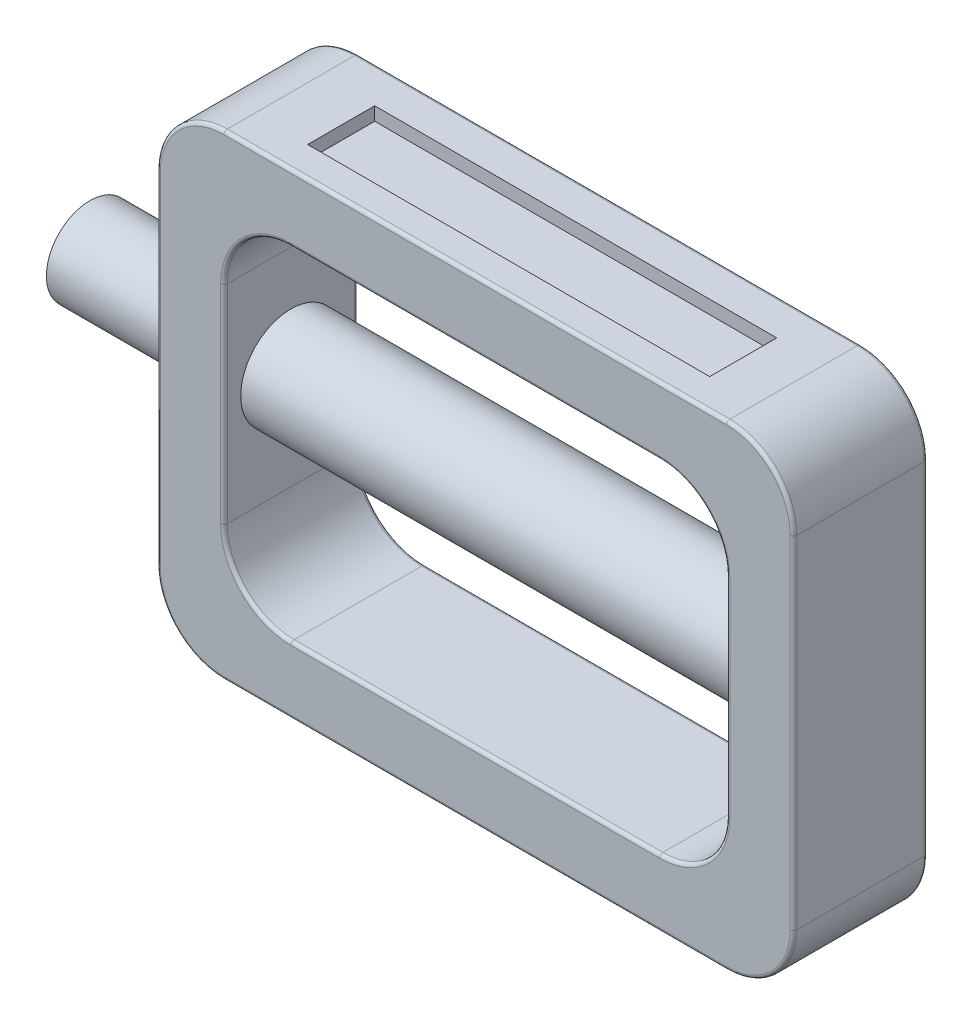
SolidWorks part; units mm, degrees
material "AISI 316 Stainless Steel Sheet (SS)"
ref_plane "Front Plane" through (0, 0, 0) normal (0, 0, 1) x (1, 0, 0)
ref_plane "Top Plane" through (0, 0, 0) normal (0, 1, 0) x (1, 0, 0)
ref_plane "Right Plane" through (0, 0, 0) normal (1, 0, 0) x (0, 0, -1)
sketch "Sketch1" plane through (0, 0, 0) normal (0, 0, 1) x (1, 0, 0)
  line L0 (0, 0) -> (0, 25.5)
  line L1 (10, 35.5) -> (85, 35.5)
  line L2 (95, 25.5) -> (95, -25.5)
  line L3 (85, -35.5) -> (10, -35.5)
  line L4 (0, -25.5) -> (0, 0)
  line L5 (0, 0) -> (95, 0) construction
  line L6 (10, 0) -> (10, 15.5)
  line L7 (20, 25.5) -> (75, 25.5)
  line L8 (85, 15.5) -> (85, 0)
  line L9 (85, 0) -> (85, -15.5)
  line L10 (75, -25.5) -> (20, -25.5)
  line L11 (10, -15.5) -> (10, 0)
  arc A0 (20, -25.5) -> (10, -15.5) centre (20, -15.5) cw
  arc A1 (85, -15.5) -> (75, -25.5) centre (75, -15.5) cw
  arc A2 (75, 25.5) -> (85, 15.5) centre (75, 15.5) cw
  arc A3 (10, 15.5) -> (20, 25.5) centre (20, 15.5) cw
  arc A4 (10, -35.5) -> (0, -25.5) centre (10, -25.5) cw
  arc A5 (95, -25.5) -> (85, -35.5) centre (85, -25.5) cw
  arc A6 (85, 35.5) -> (95, 25.5) centre (85, 25.5) cw
  arc A7 (0, 25.5) -> (10, 35.5) centre (10, 25.5) cw
  point P19 (85, 25.5)
  point P22 (10, 25.5)
  point P25 (0, -35.5)
  point P28 (95, -35.5)
  point P33 (0, 35.5)
  dimension "D6" = 10
  dimension "D1" = 95
  dimension "D2" = 35.5
  dimension "D3" = 25.5
  dimension "D4" = 75
  dimension "D5" = 10
extrude "Boss-Extrude1" add sketch "Sketch1" along normal blind 20
sketch "Sketch2" plane through (0, 0, 0) normal (1, 0, 0) x (0, 0, -1)
  line L0 (-20, 0) -> (0, 0) construction
  line L1 (-10, 25.5) -> (-10, -25.5) construction
  line L2 (-20, 25.5) -> (0, 25.5) construction
  line L3 (-20, -25.5) -> (0, -25.5) construction
  circle A0 centre (-10, 0) radius 7.5
  dimension "D1" = 15
  dimension "D2" = 10
extrude "Boss-Extrude2" add sketch "Sketch2" along normal up to surface (85 mm away) up to face at (85, 0, 10)
sketch "Sketch4" plane through (0, 0, 0) normal (1, 0, 0) x (0, 0, -1)
  circle A0 centre (-10, 0) radius 6.5
  dimension "D1" = 13
extrude "Boss-Extrude3" add sketch "Sketch4" against normal blind 20
sketch "Sketch5" plane through (0, -35.5, 0) normal (0, -1, 0) x (1, 0, 0)
  line L0 (10, 20) -> (10, 0) construction
  line L1 (18, 15.5) -> (78, 15.5)
  line L2 (18, 15.5) -> (18, 5.5)
  line L3 (18, 5.5) -> (78, 5.5)
  line L4 (78, 15.5) -> (78, 5.5)
  line L6 (10, 20) -> (85, 20) construction
  dimension "D1" = 10
  dimension "D2" = 60
  dimension "D3" = 8
  dimension "D4" = 4.5
extrude "Cut-Extrude1" cut sketch "Sketch5" against normal blind 2
mirror "Mirror1" about plane through (0, 0, 0) normal (0, 1, 0) of "Cut-Extrude1"
fillet "Fillet1" radius 0.5 16 edges at (92.0711, 32.5711, 0) (92.0711, -32.5711, 0) (47.5, -35.5, 0) (2.9289, -32.5711, 0) (0, 0, 0) (2.9289, 32.5711, 0) (92.0711, 32.5711, 20) (92.0711, -32.5711, 20) (47.5, -35.5, 20) (2.9289, -32.5711, 20) (0, 0, 20) (2.9289, 32.5711, 20) (95, 0, 0) (95, 0, 20) (47.5, 35.5, 0) (47.5, 35.5, 20)
fillet "Fillet2" radius 0.5 16 edges at (12.9289, -22.5711, 0) (10, 0, 0) (12.9289, 22.5711, 0) (47.5, 25.5, 0) (82.0711, 22.5711, 0) (82.0711, -22.5711, 0) (12.9289, -22.5711, 20) (10, 0, 20) (12.9289, 22.5711, 20) (47.5, 25.5, 20) (82.0711, 22.5711, 20) (82.0711, -22.5711, 20) (85, 0, 0) (85, 0, 20) (47.5, -25.5, 0) (47.5, -25.5, 20)
